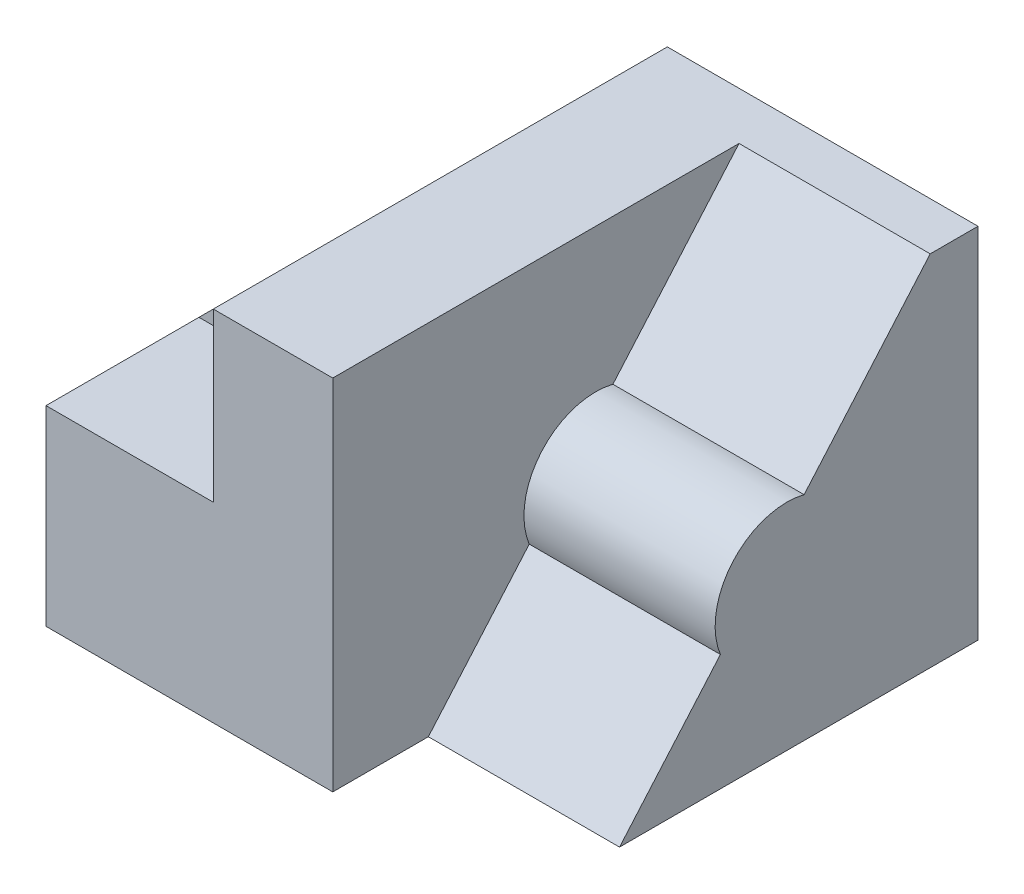
SolidWorks part; units mm, degrees
material "Brass"
ref_plane "Front Plane" through (0, 0, 0) normal (0, 0, 1) x (1, 0, 0)
ref_plane "Top Plane" through (0, 0, 0) normal (0, 1, 0) x (1, 0, 0)
ref_plane "Right Plane" through (0, 0, 0) normal (1, 0, 0) x (0, 0, -1)
sketch "Sketch1" plane through (0, 0, 0) normal (1, 0, 0) x (0, 0, -1)
  line L1 (47.5, 37.5) -> (-47.5, 37.5)
  line L2 (47.5, 37.5) -> (47.5, -37.5)
  line L3 (47.5, -37.5) -> (-47.5, -37.5)
  line L4 (-47.5, 37.5) -> (-47.5, -37.5)
  line L5 (47.5, 37.5) -> (-47.5, -37.5) construction
  line L6 (47.5, -37.5) -> (-47.5, 37.5) construction
  point P0 (0, 0)
  dimension "D1" = 75
  dimension "D2" = 95
extrude "Boss-Extrude1" add sketch "Sketch1" along normal blind 100
sketch "Sketch2" plane through (100, 0, 0) normal (1, 0, 0) x (0, 0, -1)
  line L0 (37.5, 37.5) -> (11.1165, 7.0575)
  line L1 (47.5, 37.5) -> (-47.5, 37.5) construction
  line L2 (-47.5, -37.5) -> (47.5, -37.5) construction
  line L7 (-47.5, 37.5) -> (-47.5, -37.5) construction
  line L8 (-47.5, -37.5) -> (-27.5, -37.5)
  line L9 (37.5, 37.5) -> (-47.5, 37.5)
  line L10 (-47.5, 37.5) -> (-47.5, -37.5)
  line L11 (-6.3957, -13.1489) -> (-27.5, -37.5)
  arc A0 (11.1165, 7.0575) -> (-6.3957, -13.1489) centre (7.5, -7.5) ccw
  dimension "D5" = 30
  dimension "D1" = 20
  dimension "D4" = 10
extrude "Cut-Extrude1" cut sketch "Sketch2" against normal blind 40 contours L8 L11 A0 L0 L9 L10
sketch "Sketch4" plane through (0, 0, 47.5) normal (0, 0, 1) x (1, 0, 0)
  line L1 (0, 37.5) -> (35, 37.5)
  line L2 (0, 37.5) -> (0, 2.5)
  line L3 (0, 2.5) -> (35, 2.5)
  line L4 (35, 37.5) -> (35, 2.5)
  dimension "D2" = 35
  dimension "D1" = 35
extrude "Cut-Extrude2" cut sketch "Sketch4" against normal through all
ref_plane "Plane2" through (0, 0, 9.5) normal (0, 0, 1) x (1, 0, 0)
sketch "Sketch14" plane through (0, 0, 9.5) normal (0, 0, 1) x (1, 0, 0)
  line L0 (35, 37.5) -> (0, 2.5)
  line L1 (0, 2.5) -> (35, 2.5)
  line L2 (0, 2.5) -> (35, 2.5) construction
  line L3 (35, 2.5) -> (35, 37.5) construction
  line L4 (35, 2.5) -> (35, 37.5)
extrude "Boss-Extrude4" add sketch "Sketch14" along normal blind 6
